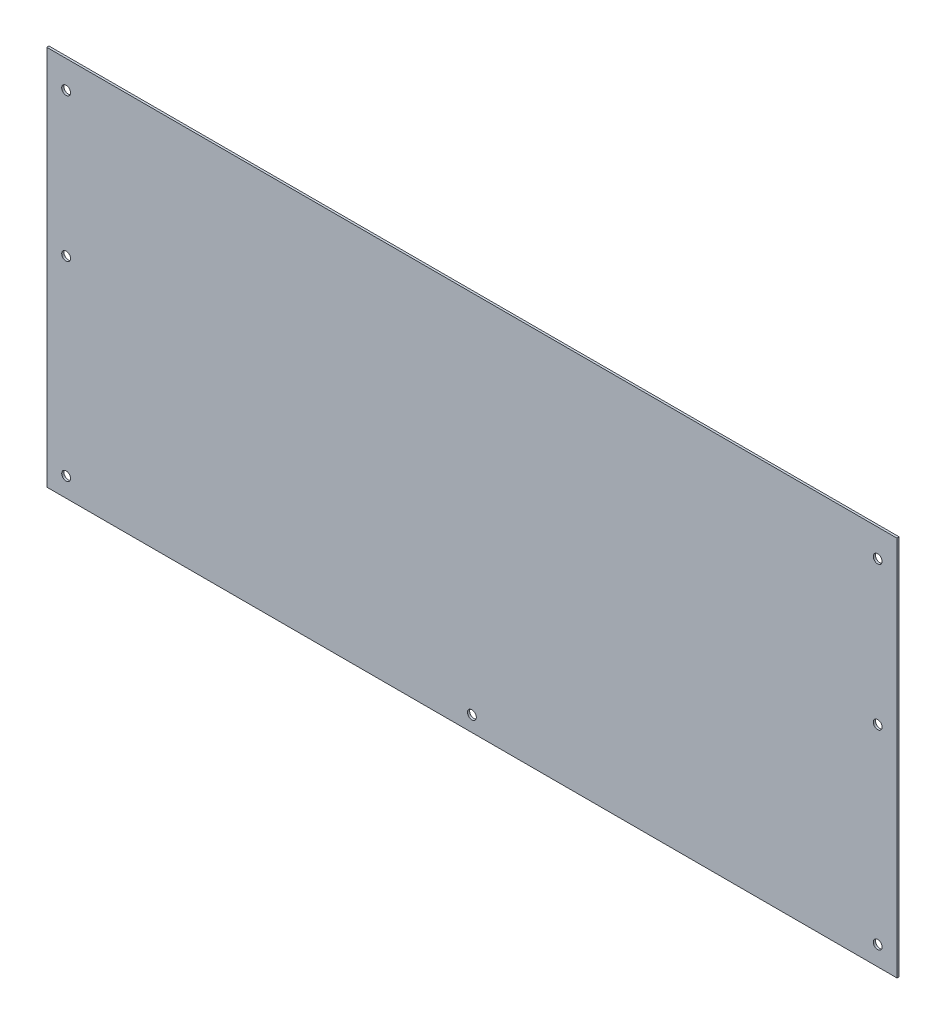
SolidWorks part; units mm, degrees
ref_plane "Front Plane" through (0, 0, 0) normal (0, 0, 1) x (1, 0, 0)
ref_plane "Top Plane" through (0, 0, 0) normal (0, 1, 0) x (1, 0, 0)
ref_plane "Right Plane" through (0, 0, 0) normal (1, 0, 0) x (0, 0, -1)
sketch "Sketch1" plane through (0, 0, 0) normal (0, 0, 1) x (1, 0, 0)
  line L0 (0, 0) -> (770, 0)
  line L1 (770, 0) -> (770, 345)
  line L2 (770, 345) -> (0, 345)
  line L3 (0, 345) -> (0, 0)
  line L4 (385, 354.9005) -> (385, -112.4967) construction
  circle A0 centre (17.5, 320) radius 4
  circle A1 centre (17.5, 17.5) radius 4
  circle A2 centre (752.5, 17.5) radius 4
  circle A3 centre (385, 13.902) radius 4
  circle A4 centre (17.5, 190) radius 4
  circle A5 centre (752.5, 190) radius 4
  circle A6 centre (752.5, 320) radius 4
  dimension "D3" = 8
  dimension "D1" = 345
  dimension "D2" = 770
  dimension "D4" = 17.5
  dimension "D5" = 17.5
  dimension "D6" = 17.5
  dimension "D7" = 25
  dimension "D8" = 17.5
extrude "Boss-Extrude1" add sketch "Sketch1" along normal blind 2
